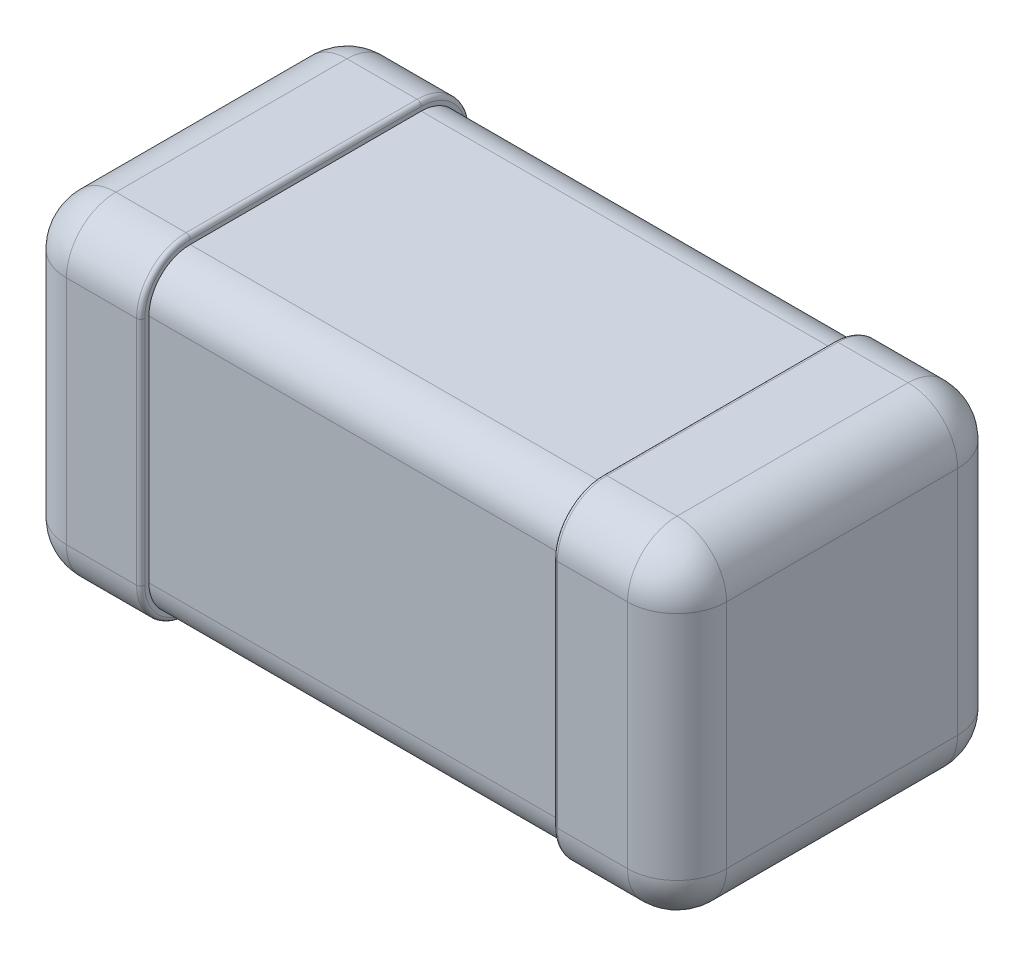
SolidWorks part; units mm, degrees
ref_plane "Front" through (0, 0, 0) normal (0, 0, 1) x (1, 0, 0)
ref_plane "Top" through (0, 0, 0) normal (0, 1, 0) x (1, 0, 0)
ref_plane "Right" through (0, 0, 0) normal (1, 0, 0) x (0, 0, -1)
sketch "Sketch1" plane through (0, 0, 0) normal (0, 1, 0) x (1, 0, 0)
  line L1 (-1.6, -0.8) -> (1.6, -0.8)
  line L2 (-1.6, -0.8) -> (-1.6, 0.8)
  line L3 (-1.6, 0.8) -> (1.6, 0.8)
  line L4 (1.6, -0.8) -> (1.6, 0.8)
  line L5 (-1.6, -0.8) -> (1.6, 0.8) construction
  line L6 (-1.6, 0.8) -> (1.6, -0.8) construction
  point P0 (0, 0)
  dimension "D1" = 1.6
  dimension "D2" = 3.2
extrude "Boss-Extrude1" add sketch "Sketch1" along normal mid plane 1.6
sketch "Sketch3" plane through (0, 0, 0) normal (1, 0, 0) x (0, 0, -1)
  line L8 (-0.76, -0.76) -> (0.76, -0.76)
  line L9 (0.76, -0.76) -> (0.76, 0.76)
  line L10 (0.76, 0.76) -> (-0.76, 0.76)
  line L11 (-0.76, 0.76) -> (-0.76, -0.76)
  line L12 (-0.76, -0.76) -> (0.76, -0.76)
  line L13 (0.76, -0.76) -> (0.76, 0.76)
  line L14 (0.76, 0.76) -> (-0.76, 0.76)
  line L15 (-0.76, 0.76) -> (-0.76, -0.76)
  dimension "D1" = 0.04
extrude "Cut-Extrude1" cut sketch "Sketch3" against normal offset from surface 0.6 and the other way offset from surface (1 mm away) 0.6 flip side to cut up to face at (-1.6, 0, 0) other way up to face at (1.6, 0, 0)
fillet "Fillet1" radius 0.2 4 edges at (0, -0.76, -0.76) (0, 0.76, -0.76) (0, -0.76, 0.76) (0, 0.76, 0.76)
fillet "Fillet2" radius 0.24 16 edges at (-1.3, -0.8, 0.8) (-1.3, 0.8, 0.8) (1.3, 0.8, 0.8) (1.3, -0.8, 0.8) (-1.3, -0.8, -0.8) (-1.3, 0.8, -0.8) (1.3, 0.8, -0.8) (1.3, -0.8, -0.8) (1.6, 0, 0.8) (1.6, 0.8, 0) (1.6, 0, -0.8) (1.6, -0.8, 0) (-1.6, 0, -0.8) (-1.6, 0.8, 0) (-1.6, 0, 0.8) (-1.6, -0.8, 0)
fillet "Fillet3" radius 0.02 16 edges at (1, 0.7297, -0.7297) (1, 0, -0.8) (1, -0.7297, -0.7297) (1, -0.8, 0) (1, -0.7297, 0.7297) (1, 0, 0.8) (1, 0.7297, 0.7297) (-1, 0.7297, -0.7297) (-1, 0, -0.8) (-1, -0.7297, -0.7297) (-1, -0.8, 0) (-1, -0.7297, 0.7297) (-1, 0, 0.8) (-1, 0.7297, 0.7297) (1, 0.8, 0) (-1, 0.8, 0)
